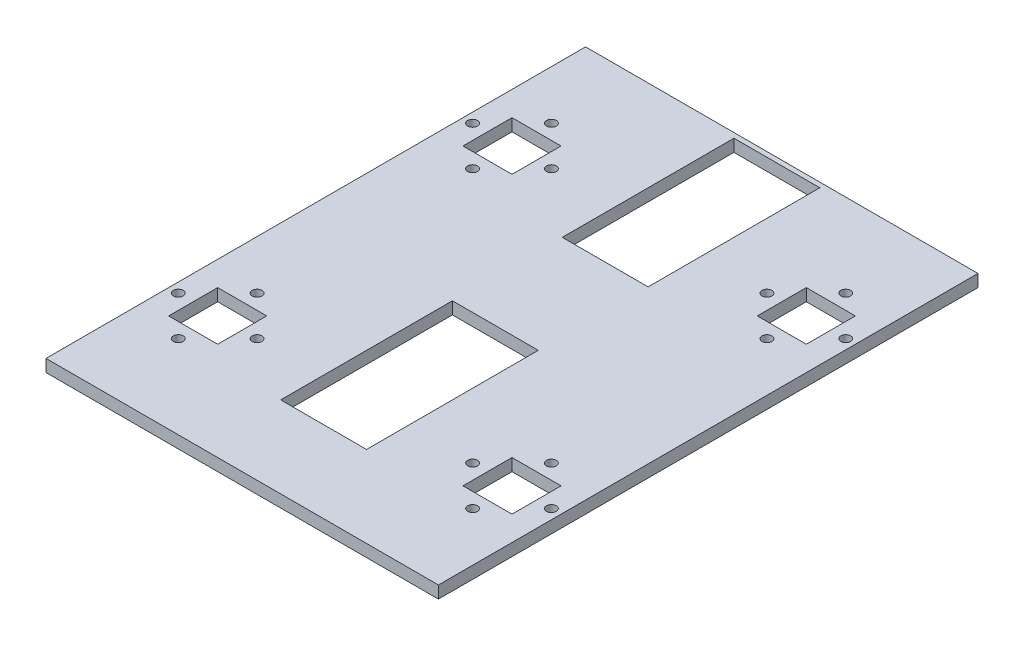
SolidWorks part; units mm, degrees
material "Balsa"
ref_plane "Front Plane" through (0, 0, 0) normal (0, 0, 1) x (1, 0, 0)
ref_plane "Top Plane" through (0, 0, 0) normal (0, 1, 0) x (1, 0, 0)
ref_plane "Right Plane" through (0, 0, 0) normal (1, 0, 0) x (0, 0, -1)
sketch "Sketch1" plane through (0, 0, 0) normal (0, 1, 0) x (1, 0, 0)
  line L1 (-101.6, 139.7) -> (101.6, 139.7)
  line L2 (-101.6, 139.7) -> (-101.6, -139.7)
  line L3 (-101.6, -139.7) -> (101.6, -139.7)
  line L4 (101.6, 139.7) -> (101.6, -139.7)
  line L5 (-101.6, 139.7) -> (101.6, -139.7) construction
  line L6 (-101.6, -139.7) -> (101.6, 139.7) construction
  point P0 (0, 0)
  dimension "D1" = 279.4
  dimension "D2" = 203.2
extrude "Boss-Extrude1" add sketch "Sketch1" along normal blind 6.35
sketch "Sketch2" plane through (0, 6.35, 0) normal (0, 1, 0) x (1, 0, 0)
  line L0 (-101.6, 139.7) -> (-101.6, -139.7) construction
  line L1 (-88.9, 88.9) -> (-63.5, 88.9)
  line L2 (-88.9, 88.9) -> (-88.9, 63.5)
  line L3 (-88.9, 63.5) -> (-63.5, 63.5)
  line L4 (-63.5, 88.9) -> (-63.5, 63.5)
  line L5 (-88.9, 88.9) -> (-63.5, 63.5) construction
  line L6 (-88.9, 63.5) -> (-63.5, 88.9) construction
  line L7 (101.6, 139.7) -> (-101.6, 139.7) construction
  line L8 (-76.2, 76.2) -> (-49.5888, 76.2) construction
  circle A0 centre (-55.8038, 76.2) radius 2.54
  circle A1 centre (-76.2, 55.8038) radius 2.54
  circle A2 centre (-96.5962, 76.2) radius 2.54
  circle A3 centre (-76.2, 96.5962) radius 2.54
  point P0 (-76.2, 76.2)
  point P22 (-76.2, 76.2)
  dimension "D4" = 5.08
  dimension "D1" = 12.7
  dimension "D2" = 50.8
  dimension "D3" = 25.4
  dimension "D5" = 7.6962
  dimension "D6" = 4
extrude "Cut-Extrude1" cut sketch "Sketch2" against normal through all both and the other way through all
pattern_linear "LPattern1" count 2 spacing 152.4 along (1, 0, 0) count 2 spacing 152.4 along (0, 0, 1) of "Cut-Extrude1"
sketch "Sketch3" plane through (0, 6.35, 0) normal (0, 1, 0) x (1, 0, 0)
  line L0 (-63.5, -76.2) -> (63.5, -76.2) construction
  line L1 (-63.5, -88.9) -> (-63.5, -63.5) construction
  line L2 (63.5, -63.5) -> (63.5, -88.9) construction
  line L3 (-63.5, 76.2) -> (63.5, 76.2) construction
  line L4 (-63.5, 63.5) -> (-63.5, 88.9) construction
  line L5 (63.5, 88.9) -> (63.5, 63.5) construction
  line L6 (-76.2, -63.5) -> (-76.2, 63.5) construction
  line L7 (-22.225, -97.536) -> (22.225, -97.536)
  line L8 (-22.225, -97.536) -> (-22.225, -8.636)
  line L9 (-22.225, -8.636) -> (22.225, -8.636)
  line L10 (22.225, -97.536) -> (22.225, -8.636)
  line L11 (-63.5, -63.5) -> (-88.9, -63.5) construction
  line L12 (-88.9, 63.5) -> (-63.5, 63.5) construction
  line L13 (-76.2, 0) -> (76.2, 0) construction
  line L14 (22.225, 76.2) -> (-22.225, 76.2) construction
  line L15 (63.5, -88.9) -> (88.9, -88.9) construction
  line L16 (76.2, 63.5) -> (76.2, -63.5) construction
  line L17 (63.5, 63.5) -> (88.9, 63.5) construction
  line L18 (88.9, -63.5) -> (63.5, -63.5) construction
  line L19 (-22.225, 137.16) -> (22.225, 137.16)
  line L20 (-22.225, 137.16) -> (-22.225, 48.26)
  line L21 (-22.225, 48.26) -> (22.225, 48.26)
  line L22 (22.225, 137.16) -> (22.225, 48.26)
  circle A0 centre (0, 76.2) radius 10.16
  circle A1 centre (0, -76.2) radius 10.16
  point P28 (0, 0)
  point P29 (0, -8.636)
  dimension "D1" = 20.32
  dimension "D2" = 20.32
  dimension "D3" = 44.45
  dimension "D4" = 88.9
  dimension "D5" = 8.636
  dimension "D6" = 44.45
  dimension "D7" = 88.9
  dimension "D8" = 15.24
extrude "Cut-Extrude2" cut sketch "Sketch3" against normal through all both and the other way through all contours L22 L19 L20 L21 A0 | L7 L10 L9 L8 A1 | A0 | A1
ref_plane "Plane1" through (0, 0, 0) normal (1, 0, 0) x (0, 0, -1)
